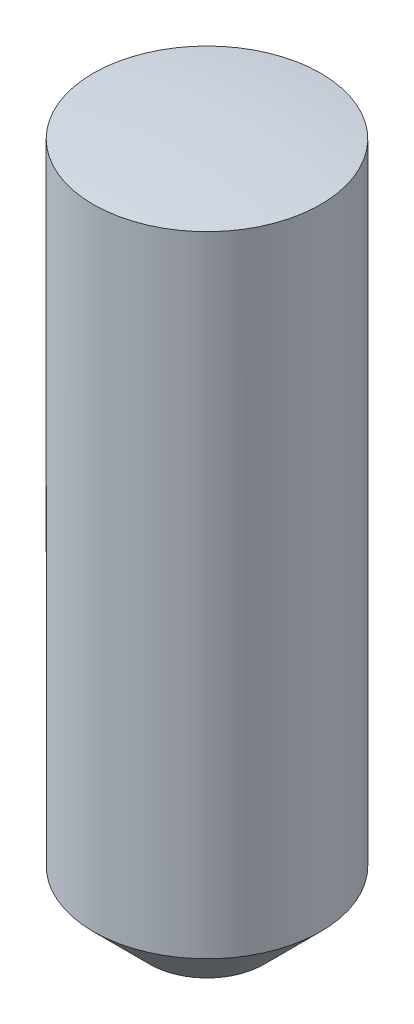
SolidWorks part; units mm, degrees
ref_plane "Front Plane" through (0, 0, 0) normal (0, 0, 1) x (1, 0, 0)
ref_plane "Top Plane" through (0, 0, 0) normal (0, 1, 0) x (1, 0, 0)
ref_plane "Right Plane" through (0, 0, 0) normal (1, 0, 0) x (0, 0, -1)
sketch "Sketch1" plane through (0, 0, 0) normal (0, 1, 0) x (1, 0, 0)
  circle A0 centre (0, 0) radius 1
  dimension "D1" = 2
extrude "Boss-Extrude 6.10mm" add sketch "Sketch1" against normal blind 6.1
chamfer "0.5 x 45 deg" distance 0.5 angle 45 1 edges at (0, -6.1, 1)
sketch "Sketch2" plane through (0, 0, 0) normal (0, 0, 1) x (1, 0, 0)
  line L0 (0, 0) -> (0, 2) construction
  line L1 (0, 2) -> (-2, 2)
  line L2 (-2, 2) -> (-2, -0.254)
  line L3 (0, 0) -> (0, 2)
  arc A0 (0, 0) -> (-2, -0.254) centre (0, -8) ccw
  dimension "D3" = 8
  dimension "D1" = 2
  dimension "D2" = 2
revolve "SR8" cut sketch "Sketch2" angle 360 about L0
